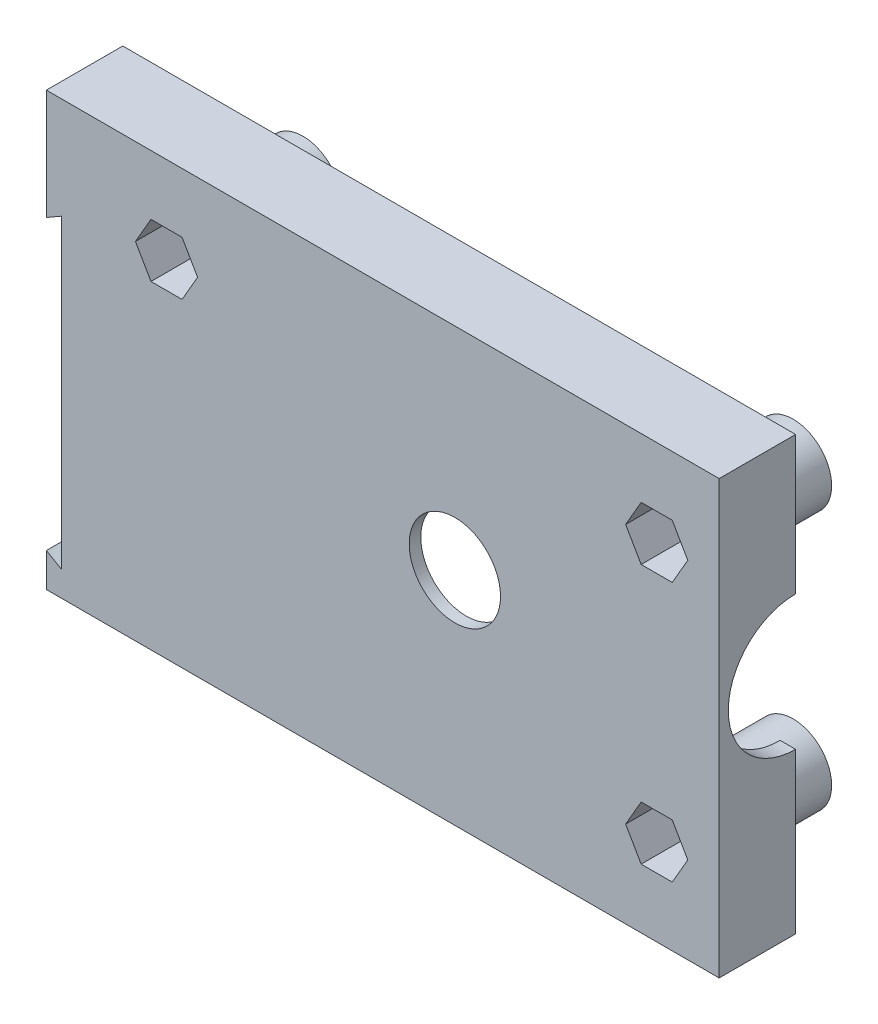
SolidWorks part; units mm, degrees
ref_plane "Front Plane" through (0, 0, 0) normal (0, 0, 1) x (1, 0, 0)
ref_plane "Top Plane" through (0, 0, 0) normal (0, 1, 0) x (1, 0, 0)
ref_plane "Right Plane" through (0, 0, 0) normal (1, 0, 0) x (0, 0, -1)
sketch "Sketch1" plane through (0, 0, 0) normal (0, 0, 1) x (1, 0, 0)
  line L1 (-35, 22.5) -> (35, 22.5)
  line L2 (-35, 22.5) -> (-35, -22.5)
  line L3 (-35, -22.5) -> (35, -22.5)
  line L4 (35, 22.5) -> (35, -22.5)
  line L5 (-35, 22.5) -> (35, -22.5) construction
  line L6 (-35, -22.5) -> (35, 22.5) construction
  point P0 (0, 0)
  dimension "D1" = 45
  dimension "D2" = 70
extrude "Boss-Extrude1" add sketch "Sketch1" along normal blind 1.2
sketch "Sketch2" plane through (0, 0, 1.2) normal (0, 0, 1) x (1, 0, 0)
  line L0 (35, -22.5) -> (35, 22.5) construction
  line L1 (-22.5, 13.5) -> (28.5, 13.5) construction
  line L2 (-22.5, 13.5) -> (-22.5, -13.5) construction
  line L3 (-22.5, -13.5) -> (28.5, -13.5) construction
  line L4 (28.5, 13.5) -> (28.5, -13.5) construction
  line L5 (-22.5, 13.5) -> (28.5, -13.5) construction
  line L6 (-22.5, -13.5) -> (28.5, 13.5) construction
  line L8 (-20.8834, 10.7) -> (-19.2668, 13.5)
  line L9 (-19.2668, 13.5) -> (-20.8834, 16.3)
  line L10 (-20.8834, 16.3) -> (-24.1166, 16.3)
  line L11 (-24.1166, 16.3) -> (-25.7332, 13.5)
  line L12 (-25.7332, 13.5) -> (-24.1166, 10.7)
  line L13 (-24.1166, 10.7) -> (-20.8834, 10.7)
  line L14 (26.8834, 10.7) -> (30.1166, 10.7)
  line L15 (30.1166, 10.7) -> (31.7332, 13.5)
  line L16 (31.7332, 13.5) -> (30.1166, 16.3)
  line L17 (30.1166, 16.3) -> (26.8834, 16.3)
  line L18 (26.8834, 16.3) -> (25.2668, 13.5)
  line L19 (25.2668, 13.5) -> (26.8834, 10.7)
  line L20 (26.8834, -16.3) -> (30.1166, -16.3)
  line L21 (30.1166, -16.3) -> (31.7332, -13.5)
  line L22 (31.7332, -13.5) -> (30.1166, -10.7)
  line L23 (30.1166, -10.7) -> (26.8834, -10.7)
  line L24 (26.8834, -10.7) -> (25.2668, -13.5)
  line L25 (25.2668, -13.5) -> (26.8834, -16.3)
  circle A0 centre (-22.5, 13.5) radius 2.8 construction
  circle A1 centre (28.5, 13.5) radius 2.8 construction
  circle A2 centre (28.5, -13.5) radius 2.8 construction
  point P0 (3, 0)
  dimension "D1" = 27
  dimension "D2" = 51
  dimension "D3" = 6.5
  dimension "D4" = 5.6
extrude "Cut-Extrude1" cut sketch "Sketch2" against normal blind 11.2
sketch "Sketch3" plane through (0, 0, 0) normal (0, 0, -1) x (-1, 0, 0)
  line L0 (-33.4, 20.9) -> (-33.4, -20.9)
  line L1 (-33.4, -20.9) -> (33.4, -20.9)
  line L2 (33.4, -20.9) -> (33.4, 20.9)
  line L3 (33.4, 20.9) -> (-33.4, 20.9)
  line L4 (-35, 22.5) -> (-35, -22.5)
  line L5 (-35, -22.5) -> (35, -22.5)
  line L6 (35, -22.5) -> (35, 22.5)
  line L7 (35, 22.5) -> (-35, 22.5)
  line L8 (-35, 22.5) -> (-35, -22.5)
  line L9 (-35, -22.5) -> (35, -22.5)
  line L10 (35, -22.5) -> (35, 22.5)
  line L11 (35, 22.5) -> (-35, 22.5)
  dimension "D1" = 0
  dimension "D2" = 1.6
extrude "Boss-Extrude2" add sketch "Sketch3" along normal blind 6.75
sketch "Sketch4" plane through (0, 0, 0) normal (0, 0, -1) x (-1, 0, 0)
  line L0 (24.1166, 10.7) -> (20.8834, 10.7) construction
  line L1 (20.8834, 10.7) -> (19.2668, 13.5) construction
  line L2 (19.2668, 13.5) -> (20.8834, 16.3) construction
  line L3 (20.8834, 16.3) -> (24.1166, 16.3) construction
  line L12 (24.1166, 16.3) -> (25.7332, 13.5) construction
  line L13 (25.7332, 13.5) -> (24.1166, 10.7) construction
  line L20 (-26.8834, -10.7) -> (-25.2668, -13.5) construction
  line L21 (-25.2668, -13.5) -> (-26.8834, -16.3) construction
  line L22 (-26.8834, -16.3) -> (-30.1166, -16.3) construction
  line L23 (-30.1166, -16.3) -> (-31.7332, -13.5) construction
  line L24 (-31.7332, -13.5) -> (-30.1166, -10.7) construction
  line L25 (-30.1166, -10.7) -> (-26.8834, -10.7) construction
  line L26 (-26.8834, 10.7) -> (-30.1166, 10.7) construction
  line L27 (-30.1166, 10.7) -> (-31.7332, 13.5) construction
  line L28 (-31.7332, 13.5) -> (-30.1166, 16.3) construction
  line L29 (-30.1166, 16.3) -> (-26.8834, 16.3) construction
  line L30 (-26.8834, 16.3) -> (-25.2668, 13.5) construction
  line L31 (-25.2668, 13.5) -> (-26.8834, 10.7) construction
  line L32 (24.1166, 10.7) -> (20.8834, 10.7)
  line L33 (20.8834, 10.7) -> (19.2668, 13.5)
  line L34 (19.2668, 13.5) -> (20.8834, 16.3)
  line L35 (20.8834, 16.3) -> (24.1166, 16.3)
  line L36 (24.1166, 16.3) -> (25.7332, 13.5)
  line L37 (25.7332, 13.5) -> (24.1166, 10.7)
  line L44 (-26.8834, -10.7) -> (-25.2668, -13.5)
  line L45 (-25.2668, -13.5) -> (-26.8834, -16.3)
  line L46 (-26.8834, -16.3) -> (-30.1166, -16.3)
  line L47 (-30.1166, -16.3) -> (-31.7332, -13.5)
  line L48 (-31.7332, -13.5) -> (-30.1166, -10.7)
  line L49 (-30.1166, -10.7) -> (-26.8834, -10.7)
  line L50 (-26.8834, 10.7) -> (-30.1166, 10.7)
  line L51 (-30.1166, 10.7) -> (-31.7332, 13.5)
  line L52 (-31.7332, 13.5) -> (-30.1166, 16.3)
  line L53 (-30.1166, 16.3) -> (-26.8834, 16.3)
  line L54 (-26.8834, 16.3) -> (-25.2668, 13.5)
  line L55 (-25.2668, 13.5) -> (-26.8834, 10.7)
  line L56 (-30.1166, 16.3) -> (-26.8834, 10.7) construction
  line L57 (-26.8834, -16.3) -> (-30.1166, -10.7) construction
  line L59 (24.1166, 10.7) -> (20.8834, 16.3) construction
  circle A0 centre (-28.5, 13.5) radius 4
  circle A1 centre (-28.5, -13.5) radius 4
  circle A3 centre (22.5, 13.5) radius 4
  dimension "D1" = 8
extrude "Boss-Extrude3" add sketch "Sketch4" along normal blind 11.5
sketch "Sketch5" plane through (0, 0, -11.5) normal (0, 0, -1) x (-1, 0, 0)
  circle A0 centre (-28.5, -13.5) radius 4 construction
  circle A2 centre (22.5, 13.5) radius 4 construction
  circle A3 centre (-28.5, 13.5) radius 4 construction
  circle A4 centre (-28.5, -13.5) radius 4
  circle A6 centre (22.5, 13.5) radius 4
  circle A7 centre (-28.5, 13.5) radius 4
  circle A8 centre (-28.5, 13.5) radius 1.75
  circle A9 centre (-28.5, -13.5) radius 1.75
  circle A11 centre (22.5, 13.5) radius 1.75
  dimension "D1" = 3.5
extrude "Boss-Extrude4" add sketch "Sketch5" along normal blind 1.5
sketch "Sketch6" plane through (35, 0, 0) normal (1, 0, 0) x (0, 0, -1)
  line L0 (6.75, 22.5) -> (6.75, -22.5) construction
  line L1 (-1.2, -22.5) -> (6.75, -22.5) construction
  circle A0 centre (6.75, 1.13) radius 7
  dimension "D1" = 14
  dimension "D2" = 23.63
extrude "Cut-Extrude2" cut sketch "Sketch6" against normal blind 11.5
sketch "Sketch7" plane through (0, 0, 1.2) normal (0, 0, 1) x (1, 0, 0)
  line L0 (-35, 11.02) -> (-33.4, 11.9438)
  line L1 (-35, 22.5) -> (-35, -22.5) construction
  line L2 (-33.4, 11.9438) -> (-33.4, -19.9038)
  line L3 (-33.4, -19.9038) -> (-35, -18.98)
  line L4 (-35, -18.98) -> (-35, 11.02)
  dimension "D1" = 120
  dimension "D2" = 120
  dimension "D3" = 30
  dimension "D4" = 1.6
  dimension "D5" = 11.48
extrude "Cut-Extrude3" cut sketch "Sketch7" against normal blind 10
sketch "Sketch8" plane through (0, 0, 1.2) normal (0, 0, 1) x (1, 0, 0)
  line L0 (35, -22.5) -> (35, 22.5) construction
  circle A0 centre (7.5, 0.5) radius 4.75
  point P2 (6.7497, 0)
  point P6 (7.5, 1.95)
  dimension "D1" = 9.5
  dimension "D2" = 27.5
  dimension "D3" = 0.5
extrude "Cut-Extrude4" cut sketch "Sketch8" against normal blind 10
